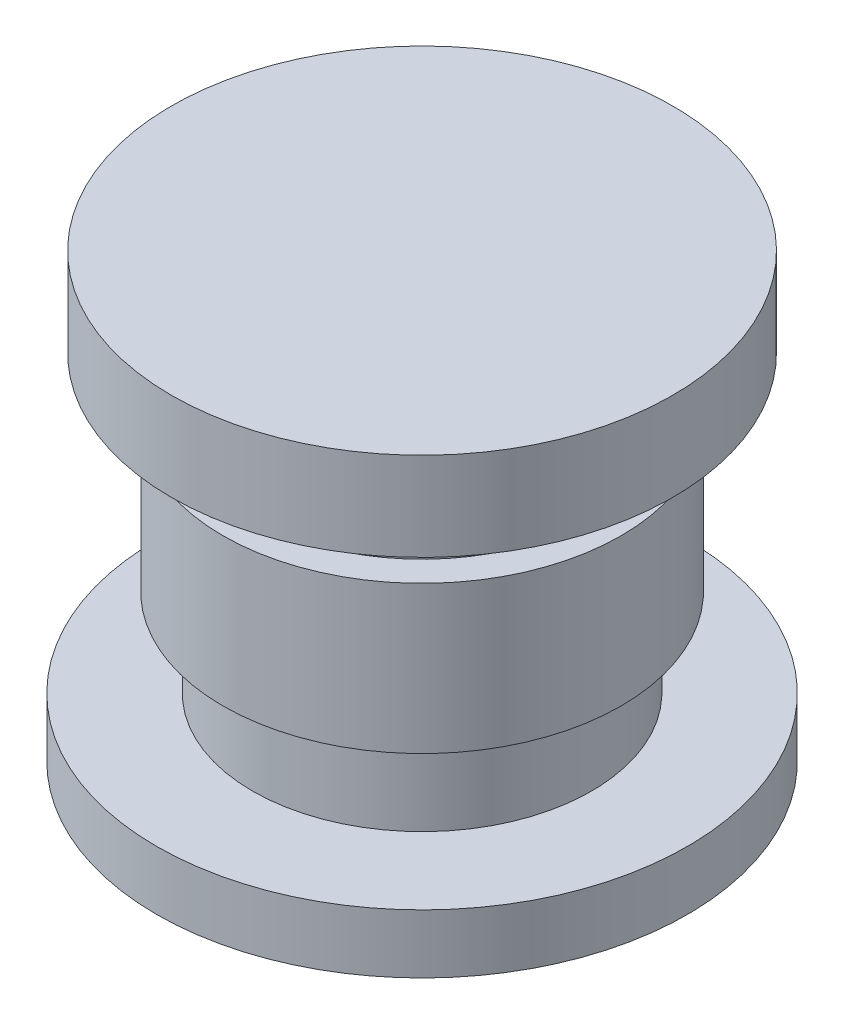
SolidWorks part; units mm, degrees
ref_plane "Front Plane" through (0, 0, 0) normal (0, 0, 1) x (1, 0, 0)
ref_plane "Top Plane" through (0, 0, 0) normal (0, 1, 0) x (1, 0, 0)
ref_plane "Right Plane" through (0, 0, 0) normal (1, 0, 0) x (0, 0, -1)
sketch "Sketch1" plane through (0, 0, 0) normal (0, 1, 0) x (1, 0, 0)
  circle A0 centre (0, 0) radius 9
  dimension "D1" = 18
extrude "Boss-Extrude1" add sketch "Sketch1" along normal blind 2
sketch "Sketch2" plane through (0, 2, 0) normal (0, 1, 0) x (1, 0, 0)
  circle A0 centre (0, 0) radius 5.75
  dimension "D1" = 11.5
extrude "Boss-Extrude2" add sketch "Sketch2" along normal blind 3
sketch "Sketch3" plane through (0, 5, 0) normal (0, 1, 0) x (1, 0, 0)
  circle A0 centre (0, 0) radius 6.75
  dimension "D1" = 13.5
extrude "Boss-Extrude3" add sketch "Sketch3" along normal blind 5
sketch "Sketch4" plane through (0, 10, 0) normal (0, 1, 0) x (1, 0, 0)
  circle A0 centre (0, 0) radius 5.75
  dimension "D1" = 11.5
extrude "Boss-Extrude4" add sketch "Sketch4" along normal blind 2
sketch "Sketch5" plane through (0, 12, 0) normal (0, 1, 0) x (1, 0, 0)
  circle A0 centre (0, 0) radius 8.5
  dimension "D1" = 17
extrude "Boss-Extrude5" add sketch "Sketch5" along normal blind 3
